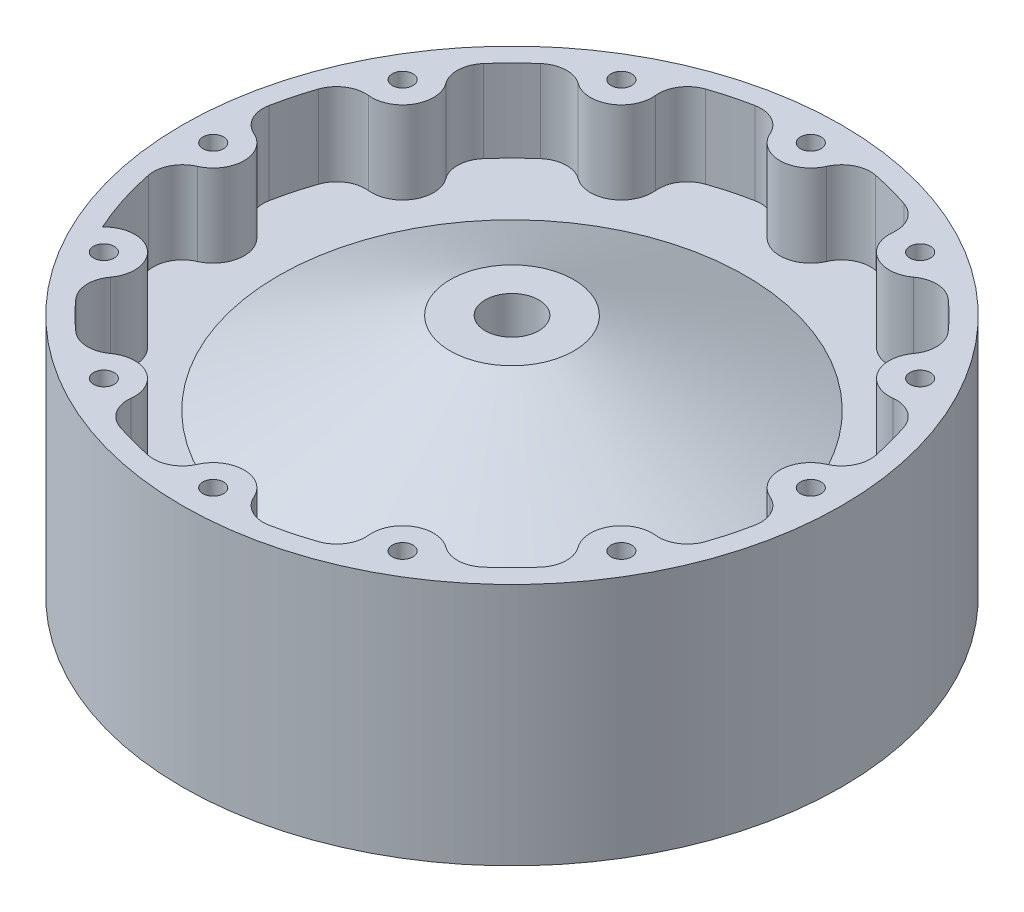
SolidWorks part; units mm, degrees
material "6061-T4 (SS)"
ref_plane "Front Plane" through (0, 0, 0) normal (0, 0, 1) x (1, 0, 0)
ref_plane "Top Plane" through (0, 0, 0) normal (0, 1, 0) x (1, 0, 0)
ref_plane "Right Plane" through (0, 0, 0) normal (1, 0, 0) x (0, 0, -1)
ref_plane "Plane1" through (0, 0, -75.0887) normal (0, 0, 1) x (1, 0, 0)
sketch "Sketch1" plane through (0, 0, 0) normal (0, 1, 0) x (1, 0, 0)
  line L1 (95.25, 0) -> (101.6, 0)
  line L2 (0, 0) -> (0, 61.9125) construction
  line L4 (101.6, 61.1187) -> (101.6, 0)
  line L6 (101.6, 61.1187) -> (8.255, 61.1187) construction
  line L8 (0, 75.0887) -> (101.6, 75.0887)
  line L9 (101.6, 75.0887) -> (101.6, 61.1187)
  line L10 (8.255, 0) -> (8.255, 75.0887)
  line L11 (8.255, 75.0887) -> (-8.255, 75.0887)
  line L12 (-8.255, 75.0887) -> (-8.255, 0)
  line L13 (-8.255, 0) -> (8.255, 0)
  line L14 (8.255, 61.1187) -> (0, 61.1187) construction
  line L15 (19.05, 75.0887) -> (71.9667, 49.6887)
  line L17 (95.25, 49.6887) -> (95.25, 75.0887)
  line L18 (95.25, 49.6887) -> (71.9667, 49.6887)
  ellipse E0 centre (0, 0) end of major axis (-95.25, 0) minor radius 61.1187
  point P18 (19.05, 75.0887)
  dimension "D4" = 13.97
  dimension "D6" = 16.51
  dimension "D7" = 6.35
  dimension "D10" = 19.05
  dimension "D2" = 101.6
  dimension "D3" = 75.0887
  dimension "D5" = 25.4
revolve "Revolve1" add sketch "Sketch1" angle 360 about L2
sketch "Sketch13" plane through (0, 0, 0) normal (0, 0, 1) x (1, 0, 0)
  line L0 (-67.9108, -66.7883) -> (66.7883, 67.9108)
  line L1 (-66.7883, -67.9108) -> (67.9108, 66.7883)
  line L2 (0, 0) -> (0, -28.3739) construction
  circle A4 centre (0, 0) radius 95.25 construction
  arc A5 (-67.9108, -66.7883) -> (-66.7883, -67.9108) centre (0, 0) ccw
  arc A6 (66.7883, 67.9108) -> (67.9108, 66.7883) centre (0, 0) cw
  dimension "D1" = 1.5875
  dimension "D2" = 135
sketch "Sketch14" plane through (0, 0, -75.0888) normal (0, 0, -1) x (-1, 0, 0)
  circle A0 centre (0, 0) radius 8.255
  circle A1 centre (0, 0) radius 8.255 construction
sketch "Sketch15" plane through (0, 0, -75.0888) normal (0, 0, -1) x (-1, 0, 0)
  circle A0 centre (0, 0) radius 95.25
  circle A3 centre (0, -92.075) radius 9.525
  circle A4 centre (0, 0) radius 101.6 construction
  circle A5 centre (0, 0) radius 95.25 construction
  circle M2 centre (0, 0) radius 95.25
  dimension "D1" = 19.05
extrude "Boss-Extrude3" add sketch "Sketch15" against normal up to body (25.4 mm away) separate body contours A3 M2
sketch "Sketch16" plane through (0, 0, -75.0888) normal (0, 0, -1) x (-1, 0, 0)
  line L0 (0, 0) -> (0, -92.075) construction
  circle A0 centre (0, -92.075) radius 3.175
  circle A2 centre (0, 0) radius 95.25 construction
  arc A3 (9.1233, -94.8121) -> (-9.1233, -94.8121) centre (0, 0) ccw construction
  dimension "D1" = 6.35
sketch "Sketch17" plane through (0, 0, -75.0888) normal (0, 0, -1) x (-1, 0, 0)
  line L0 (0, 0) -> (0, -101.6) construction
  line L2 (0, -95.25) -> (16.9112, -95.25) construction
  line L3 (0, -82.55) -> (13.8103, -82.55) construction
  line L4 (0, -88.9) -> (10.3365, -88.9) construction
  circle A0 centre (0, -92.075) radius 3.175
  circle A1 centre (0, 0) radius 101.6 construction
  arc A3 (9.1233, -94.8121) -> (-9.1233, -94.8121) centre (0, -92.075) ccw construction
  dimension "D1" = 6.35
  dimension "D2" = 6.35
extrude "Cut-Extrude5" cut sketch "Sketch17" against normal blind 25.4
pattern_circular "CirPattern5" count 12 over 360 about axis through (0, 0, 0) along (0, 0, 1) of "Boss-Extrude3", "Cut-Extrude5"
fillet "Fillet2" radius 8.89 23 edges at (-9.1233, 94.8121, -62.3887) (9.1233, 94.8121, -62.3887) (39.505, 86.6713, -62.3887) (55.307, 77.548, -62.3887) (77.548, 55.307, -62.3887) (86.6713, 39.505, -62.3887) (94.8121, 9.1233, -62.3887) (94.8121, -9.1233, -62.3887) (86.6713, -39.505, -62.3887) (77.548, -55.307, -62.3887) (55.307, -77.548, -62.3887) (39.505, -86.6713, -62.3887) (9.1233, -94.8121, -62.3887) (-9.1233, -94.8121, -62.3887) (-39.505, -86.6713, -62.3887) (-55.307, -77.548, -62.3887) (-77.548, -55.307, -62.3887) (-86.6713, -39.505, -62.3887) (-94.8121, -9.1233, -62.3887) (-94.8121, 9.1233, -62.3887) (-77.548, 55.307, -62.3887) (-55.307, 77.548, -62.3887) (-39.505, 86.6713, -62.3887)
move or copy body "Body-Move/Copy1" bodies to move or copy 124 copy no rotation origin (0, 0, -37.5444) rotation axis (1, 0, 0) rotation angle 90
equation "\"D7@Sketch1\"= .25"
equation "\"D1@Plane1\"= \"D3@Sketch1\""
